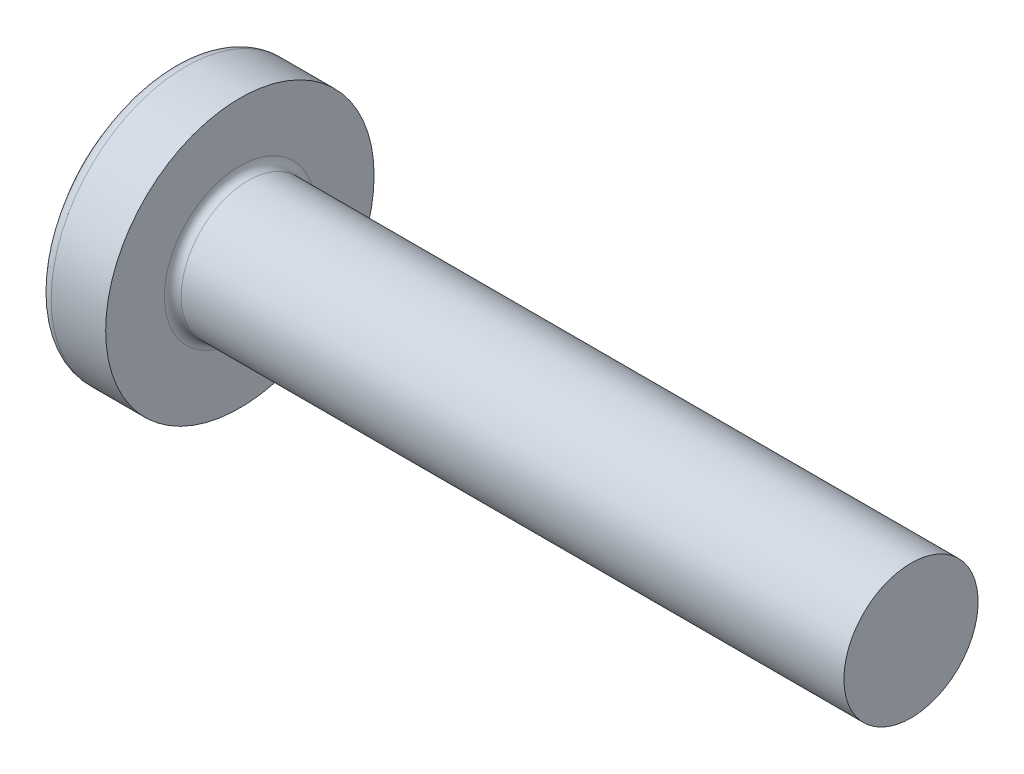
SolidWorks part; units mm, degrees
ref_plane "Plane1" through (0, 0, 0) normal (0, 0, 1) x (1, 0, 0)
ref_plane "Plane2" through (0, 0, 0) normal (0, 1, 0) x (1, 0, 0)
ref_plane "Plane3" through (0, 0, 0) normal (1, 0, 0) x (0, 0, -1)
sketch "BodySke" plane through (0, 0, 0) normal (0, 0, 1) x (1, 0, 0)
  line L0 (1.3, 0.8) -> (1.3, 1.6)
  line L1 (1.475, 6.35) -> (1.475, -3.175) construction
  line L2 (-25.4, 0) -> (127, 0) construction
  line L3 (9.3, 0) -> (0, 0)
  line L4 (1.3, 0.8) -> (9.3, 0.8)
  line L5 (9.3, 0.8) -> (9.3, 0)
  line L6 (0.6507, 1.6) -> (1.3, 1.6)
  line L8 (1.3, 6.35) -> (1.3, -3.175) construction
  arc A0 (0.5326, 1.5426) -> (0, 0) centre (2.5, 0) ccw
  arc A2 (0.5326, 1.5426) -> (0.6507, 1.6) centre (0.6507, 1.45) cw
  dimension "Head_crown_rad" = 2.5
  dimension "Head_fillet_rad" = 0.15
  dimension "Length" = 8
  dimension "Head_ht" = 1.3
  dimension "Head_dia" = 3.2
  dimension "Advance" = 0.35
  dimension "Thread_nom" = 8
  dimension "Diameter" = 1.6
revolve "Base-Revolve" add sketch "BodySke"
cosmetic thread "ThreadCosmetic" [suppressed]
fillet "Fillet1" radius 0.1 1 edges at (1.3, 0, 0.8)
sketch "Sketch3" plane through (0, 0, 0) normal (1, 0, 0) x (0, 0, -1)
  line L0 (0.24, -0.8) -> (-0.24, -0.8)
  line L1 (0.24, -0.8) -> (0.24, 0.8)
  line L2 (-0.24, 0.8) -> (0.24, 0.8)
  line L3 (-0.24, 0.8) -> (-0.24, -0.8)
  dimension "Cross_dia" = 1.6
  dimension "D1" = 0.8
  dimension "Cross_width" = 0.48
  dimension "D2" = 0.24
ref_plane "Plane4" through (0.9, 0, 0) normal (1, 0, 0) x (0, 0, -1)
sketch "Sketch4" plane through (0.9, 0, 0) normal (1, 0, 0) x (0, 0, -1)
  line L0 (0.24, -0.3513) -> (-0.24, -0.3513)
  line L1 (0.24, -0.3513) -> (0.24, 0.3513)
  line L2 (-0.24, 0.3513) -> (0.24, 0.3513)
  line L3 (-0.24, 0.3513) -> (-0.24, -0.3513)
  dimension "D1" = 0.48
  dimension "D2" = 0.7026
  dimension "D3" = 0.24
  dimension "D4" = 0.3513
loft "Recess" cut profiles "Sketch3", "Sketch4"
pattern_circular "RecPat" count 2 every 90 about axis through (0, 0, 0) along (1, 0, 0) of "Recess"
sketch "RecCorSke" plane through (0, 0, 0) normal (0, 0, 1) x (1, 0, 0)
  line L0 (-3.175, 0) -> (15.875, 0) construction
  line L1 (-25.4, 0) -> (127, 0) construction
  line L2 (0, 0) -> (0, 0.4184)
  line L3 (0, 0.4184) -> (0.9, 0.3555)
  line L4 (0.9, 0.3555) -> (1.0155, 0)
  line L5 (1.0155, 0) -> (0, 0)
  dimension "Diameter" = 0.711
  dimension "Depth" = 0.9
  dimension "Draft_angle" = 4
  dimension "Bottom_angle" = 18
revolve "RecessCore" cut sketch "RecCorSke" angle 360 about L0
sketch "ThdSchSke" plane through (0, 0, 0) normal (0, 0, 1) x (1, 0, 0)
  line L0 (2, -0.601) -> (1.8607, -0.8)
  line L1 (2, -0.601) -> (2.1393, -0.8)
  line L2 (2.1393, -0.8) -> (2.1393, -1)
  line L3 (-3.175, 0) -> (5.1513, 0) construction
  line L5 (2.1393, -1) -> (1.8607, -1)
  line L6 (1.8607, -1) -> (1.8607, -0.8)
  dimension "Diameter" = 1.6
  dimension "SideAngle" = 55
  dimension "VeeAngle" = 70
  dimension "Thread_minor" = 1.202
  dimension "Overcut" = 2
  dimension "Start" = 2
revolve "ThreadSchematic" [suppressed] cut sketch "ThdSchSke" angle 360 about L3
pattern_linear "ThdSchPat" [suppressed]
equation "\"D1@Sketch3\" = \"Cross_dia@Sketch3\" / 2"
equation "\"D2@Sketch3\" = \"Cross_width@Sketch3\" / 2"
equation "\"Depth@RecCorSke\" = \"Cross_depth@Plane4\""
equation "\"D1@Sketch4\" = \"Cross_width@Sketch3\""
equation "\"D2@Sketch4\" = \"Cross_dia@Sketch3\" - 2.0 * \"Cross_depth@Plane4\" * tan(26.5  * 0.017453292)"
equation "\"D3@Sketch4\" = \"D1@Sketch4\" / 2"
equation "\"D4@Sketch4\" = \"D2@Sketch4\" / 2"
equation "\"Thread_length@ThreadCosmetic\" = ((sgn( (\"Length@BodySke\" - \"Advance@BodySke\" * 2.0 ) - \"Thread_nom@BodySke\" )-1)*( (\"Length@BodySke\" - \"Advance@BodySke\" * 2.0 ) - \"Thread_nom@BodySke\" ))/-2+ \"Thread_nom@BodySke\""
equation "\"Thread_minor@ThdSchSke\" = \"Thread_minor@ThreadCosmetic\""
equation "\"Diameter@ThdSchSke\" = \"Diameter@BodySke\""
equation "\"Overcut@ThdSchSke\" = \"Diameter@BodySke\" * 1.25"
equation "\"Start@ThdSchSke\" = \"Head_ht@BodySke\" + \"Length@BodySke\" - \"Thread_length@ThreadCosmetic\"  '---Non-countersunk---"
equation "\"Num_threads@ThdSchPat\" = int( \"Thread_length@ThreadCosmetic\" / \"Advance@BodySke\" + 0.999 )  + 1"
equation "\"Advance@ThdSchPat\" = \"Thread_length@ThreadCosmetic\" /  (\"Num_threads@ThdSchPat\" - 1) 'relax it"
